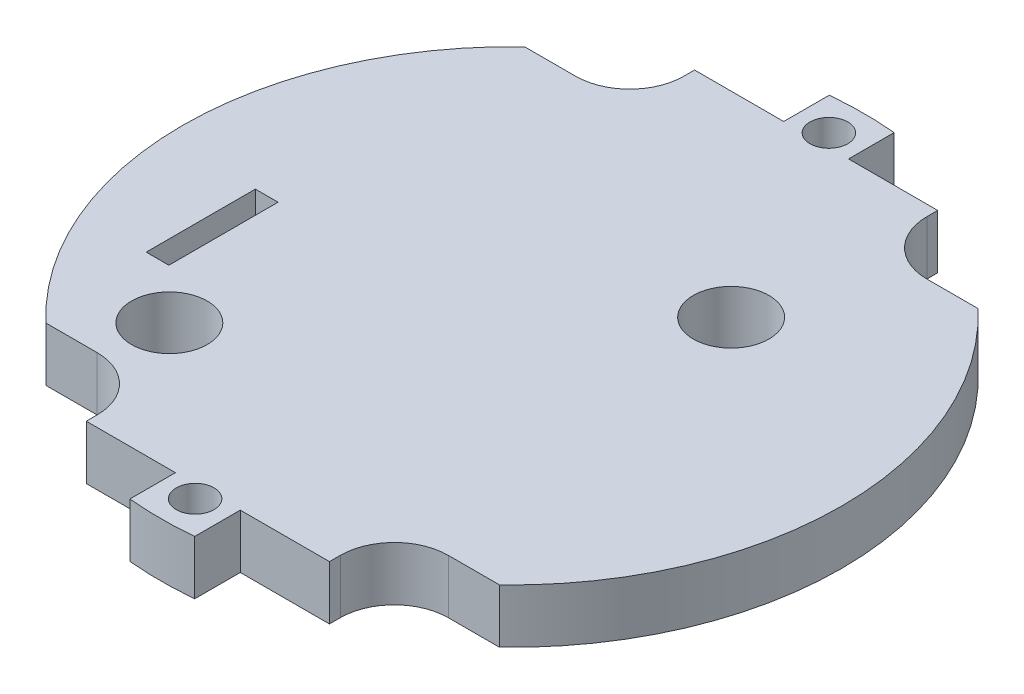
SolidWorks part; units mm, degrees
ref_plane "Front Plane" through (0, 0, 0) normal (0, 0, 1) x (1, 0, 0)
ref_plane "Top Plane" through (0, 0, 0) normal (0, 1, 0) x (1, 0, 0)
ref_plane "Right Plane" through (0, 0, 0) normal (1, 0, 0) x (0, 0, -1)
sketch "Sketch2" plane through (0, 0, 0) normal (0, 1, 0) x (1, 0, 0)
  line L0 (0, 32.5) -> (0, -32.5) construction
  line L1 (3, 32.3612) -> (3, 28.1412)
  line L2 (32.5, 0) -> (-32.5, 0) construction
  line L3 (3, 28.1412) -> (11.25, 28.1412)
  line L4 (11.25, 28.1412) -> (11.25, 22.1412)
  line L5 (11.25, 22.1412) -> (-11.25, 22.1412)
  line L6 (-3, 28.1412) -> (-11.25, 28.1412)
  line L7 (-3, 32.3612) -> (-3, 28.1412)
  line L8 (-11.25, 28.1412) -> (-11.25, 22.1412)
  line L9 (-11.25, -28.1412) -> (-11.25, -22.1412)
  line L10 (-3, -32.3612) -> (-3, -28.1412)
  line L11 (-3, -28.1412) -> (-11.25, -28.1412)
  line L12 (11.25, -22.1412) -> (-11.25, -22.1412)
  line L13 (11.25, -28.1412) -> (11.25, -22.1412)
  line L14 (3, -28.1412) -> (11.25, -28.1412)
  line L15 (3, -32.3612) -> (3, -28.1412)
  line L16 (-11.25, 22.1412) -> (-20.9765, 22.1412)
  line L17 (11.25, 22.1412) -> (20.9765, 22.1412)
  line L18 (-11.25, -22.1412) -> (-20.9765, -22.1412)
  line L19 (11.25, -22.1412) -> (20.9765, -22.1412)
  arc A0 (-3, -32.3612) -> (3, -32.3612) centre (0, 0) ccw
  circle A1 centre (0, 29.32) radius 1.75
  circle A2 centre (0, -29.32) radius 1.75
  circle A3 centre (0, -29.32) radius 1.75
  arc A5 (-20.9765, 22.1412) -> (-20.9765, -22.1412) centre (0, 0) ccw
  arc A6 (3, 32.3612) -> (-3, 32.3612) centre (0, 0) ccw
  arc A7 (20.9765, -22.1412) -> (20.9765, 22.1412) centre (0, 0) ccw
  point P20 (0, 22.1412)
  point P29 (0, -22.1412)
  dimension "D1" = 65
  dimension "D2" = 3.5
  dimension "D8" = 30.5
  dimension "D9" = 30.5
  dimension "D3" = 3.18
  dimension "D4" = 11.25
  dimension "D5" = 3
  dimension "D6" = 4.22
  dimension "D7" = 6
extrude "Boss-Extrude1" add sketch "Sketch2" along normal blind 5 contours L19 A0 L17 L5 L16 L18 L12 | L1 A0 L7 L6 L8 L5 L4 L3 A1 | L10 A0 L15 L14 L13 L12 L9 L11 A2
fillet "Fillet1" radius 5 4 edges at (11.25, 2.5, 22.1412) (-11.25, 2.5, 22.1412) (-11.25, 2.5, -22.1412) (11.25, 2.5, -22.1412)
sketch "Sketch3" plane through (0, 5, 0) normal (0, 1, 0) x (1, 0, 0)
  line L0 (16.25, -22.1412) -> (20.9765, -22.1412) construction
  line L1 (-20.9765, 22.1412) -> (-16.25, 22.1412) construction
  line L2 (-20.9765, -22.1412) -> (-16.25, -22.1412) construction
  line L3 (-19.9265, -6.7712) -> (-22.0265, -6.7712) construction
  line L4 (-20.9765, -10.5812) -> (-20.9765, -2.9612) construction
  line L5 (-19.9265, -11.8212) -> (-22.0265, -11.8212)
  line L6 (-19.9265, -11.8212) -> (-19.9265, -1.7212)
  line L7 (-19.9265, -1.7212) -> (-22.0265, -1.7212)
  line L8 (-22.0265, -11.8212) -> (-22.0265, -1.7212)
  circle A0 centre (10.2535, 10.0212) radius 3.5
  circle A1 centre (-15.2935, -16.4112) radius 3.5
  point P0 (-17.2465, 18.0212)
  point P1 (-20.9765, -10.5812)
  point P2 (14.7065, -14.4112)
  point P15 (-20.9765, -5.5012)
  point P17 (-20.9765, -8.0412)
  point P18 (-20.9765, -2.9612)
  point P23 (-20.9765, -2.1414)
  point P24 (-20.9765, -10.5812)
  point P29 (-20.9765, -2.9612)
  point P30 (-23.5602, -6.7712)
  point P31 (-18.3929, -6.7712)
  dimension "D6" = 7
  dimension "D7" = 7
  dimension "D1" = 6.27
  dimension "D2" = 7.73
  dimension "D3" = 4.12
  dimension "D4" = 3.73
  dimension "D5" = 11.56
  dimension "D8" = 8
  dimension "D9" = 27.5
  dimension "D10" = 30
  dimension "D11" = 2
  dimension "D12" = 2.54
  dimension "D13" = 2.54
  dimension "D14" = 1.27
  dimension "D15" = 2.54
  dimension "D16" = 2.1
  dimension "D17" = 10.1
extrude "Cut-Extrude1" cut sketch "Sketch3" against normal through all
